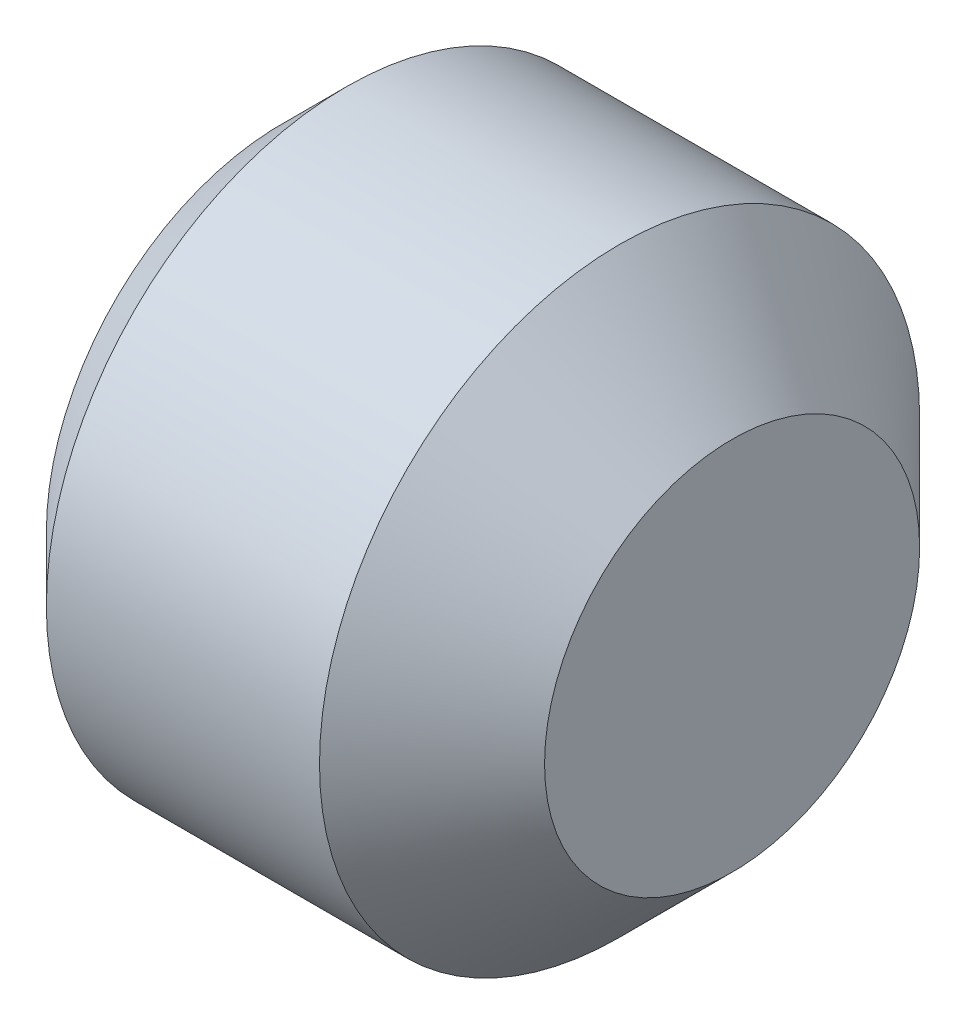
SolidWorks part; units mm, degrees
ref_plane "正面" through (0, 0, 0) normal (0, 0, 1) x (1, 0, 0)
ref_plane "平面" through (0, 0, 0) normal (0, 1, 0) x (1, 0, 0)
ref_plane "右側面" through (0, 0, 0) normal (1, 0, 0) x (0, 0, -1)
ref_plane "平面1" through (0, 0, 0) normal (0, 0, 1) x (1, 0, 0)
sketch "ｽｹｯﾁ1" plane through (0, 0, 0) normal (0, 0, 1) x (1, 0, 0)
  line L0 (-3, 0) -> (-3, 1.5705)
  line L1 (-3, 1.5705) -> (-2.5705, 2)
  line L2 (-2.5705, 2) -> (-0.75, 2)
  line L3 (-0.75, 2) -> (0, 1.25)
  line L4 (0, 1.25) -> (0, 0)
  line L5 (0, 0) -> (-3, 0)
  line L6 (0, 0) -> (-3, 0) construction
revolve "回転1" add sketch "ｽｹｯﾁ1" angle 360 about L6
cosmetic thread "ねじ山1" parameters "D1"=3, "D2"=3.141
ref_plane "平面2" through (-3, 0, 0) normal (-1, 0, 0) x (0, 0, 1)
sketch "ｽｹｯﾁ2" plane through (-3, 0, 0) normal (-1, 0, 0) x (0, 0, 1)
  line L0 (0.5774, -1) -> (1.1547, 0)
  line L1 (1.1547, 0) -> (0.5774, 1)
  line L2 (0.5774, 1) -> (-0.5774, 1)
  line L3 (-0.5774, 1) -> (-1.1547, 0)
  line L4 (-1.1547, 0) -> (-0.5774, -1)
  line L5 (-0.5774, -1) -> (0.5774, -1)
extrude "ｶｯﾄ - 押し出し1" cut sketch "ｽｹｯﾁ2" against normal blind 1.5
ref_plane "平面3" through (0, 0, 0) normal (0, 0, 1) x (1, 0, 0)
sketch "ｽｹｯﾁ3" plane through (0, 0, 0) normal (0, 0, 1) x (1, 0, 0)
  line L0 (-1.5, 0) -> (-1.5, 1)
  line L1 (-1.5, 1) -> (-0.9226, 0)
  line L2 (-0.9226, 0) -> (-1.5, 0)
  line L3 (-0.9226, 0) -> (-1.5, 0) construction
revolve "ｶｯﾄ - 回転1" cut sketch "ｽｹｯﾁ3" angle 360 about L3
